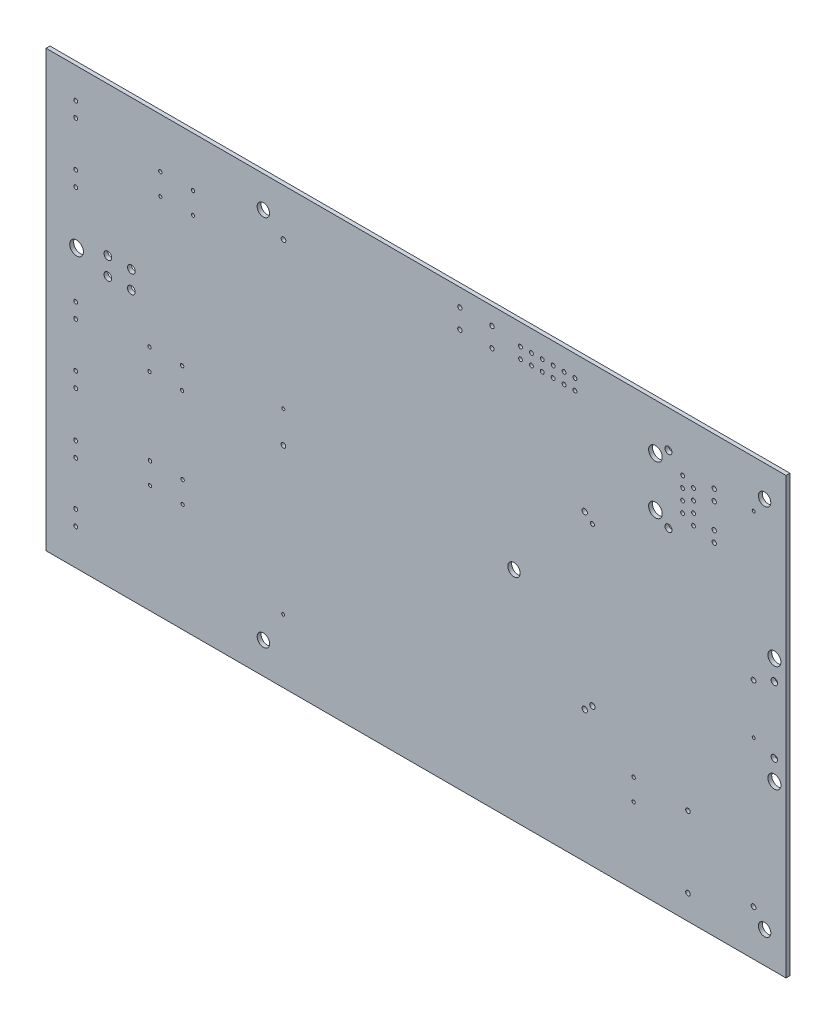
SolidWorks part; units mm, degrees
ref_plane "Front Plane" through (0, 0, 0) normal (0, 0, 1) x (1, 0, 0)
ref_plane "Top Plane" through (0, 0, 0) normal (0, 1, 0) x (1, 0, 0)
ref_plane "Right Plane" through (0, 0, 0) normal (1, 0, 0) x (0, 0, -1)
ref_plane "Plane1" through (0, 0, 0.9093) normal (0, 0, 1) x (1, 0, 0)
sketch "Sketch1" plane through (0, 0, 0.9093) normal (0, 0, 1) x (1, 0, 0)
  line L0 (114.3, 73.66) -> (287.02, 73.66)
  line L1 (287.02, 73.66) -> (287.02, 175.26)
  line L2 (287.02, 175.26) -> (114.3, 175.26)
  line L3 (114.3, 175.26) -> (114.3, 73.66)
  line L4 (114.3, 124.46) -> (287.02, 124.46) construction
  circle A1 centre (279.49, 164.285) radius 0.35
  circle A2 centre (270.256, 164.211) radius 0.51
  circle A3 centre (265.43, 161.925) radius 0.445
  circle A4 centre (262.89, 163.195) radius 0.445
  circle A5 centre (270.256, 161.671) radius 0.51
  circle A6 centre (265.43, 156.845) radius 0.445
  circle A7 centre (265.43, 159.385) radius 0.445
  circle A8 centre (270.256, 155.829) radius 0.51
  circle A9 centre (262.89, 160.655) radius 0.445
  circle A10 centre (262.89, 158.115) radius 0.445
  circle A11 centre (237.744, 167.767) radius 0.45
  circle A12 centre (237.744, 170.307) radius 0.45
  circle A13 centre (235.204, 167.767) radius 0.45
  circle A14 centre (232.664, 170.307) radius 0.45
  circle A15 centre (230.124, 170.307) radius 0.45
  circle A16 centre (235.204, 170.307) radius 0.45
  circle A17 centre (259.588, 166.624) radius 0.815
  circle A18 centre (232.664, 167.767) radius 0.45
  circle A19 centre (256.54, 164.465) radius 1.59
  circle A20 centre (227.584, 167.767) radius 0.45
  circle A21 centre (230.124, 167.767) radius 0.45
  circle A22 centre (284.3022, 136.906) radius 1.524
  circle A23 centre (284.3022, 132.207) radius 0.7493
  circle A24 centre (279.49, 118.485) radius 0.35
  circle A25 centre (270.256, 153.289) radius 0.51
  circle A26 centre (265.43, 154.305) radius 0.445
  circle A27 centre (279.44, 130.085) radius 0.55
  circle A28 centre (284.3022, 112.014) radius 1.524
  circle A29 centre (284.3022, 116.713) radius 0.7493
  circle A30 centre (279.44, 84.285) radius 0.55
  circle A31 centre (264.1346, 79.375) radius 0.5334
  circle A33 centre (262.89, 155.575) radius 0.445
  circle A34 centre (256.54, 153.035) radius 1.59
  circle A35 centre (259.588, 150.876) radius 0.815
  circle A36 centre (240.03, 144.46) radius 0.625
  circle A37 centre (241.83, 142.86) radius 0.475
  circle A38 centre (264.1346, 96.0374) radius 0.5334
  circle A39 centre (251.46, 96.48) radius 0.4
  circle A40 centre (251.46, 91.48) radius 0.375
  circle A41 centre (241.83, 106.06) radius 0.625
  circle A42 centre (240.03, 104.46) radius 0.625
  circle A43 centre (227.584, 170.307) radius 0.45
  circle A44 centre (225.044, 170.307) radius 0.45
  circle A45 centre (225.044, 167.767) radius 0.45
  circle A46 centre (218.38, 171.16) radius 0.495
  circle A47 centre (210.88, 171.16) radius 0.495
  circle A49 centre (218.38, 166.66) radius 0.495
  circle A50 centre (210.88, 166.66) radius 0.495
  circle A51 centre (169.715, 164.285) radius 0.55
  circle A52 centre (148.59, 163.6366) radius 0.4
  circle A53 centre (148.59, 158.6366) radius 0.375
  circle A54 centre (140.97, 163.6366) radius 0.4
  circle A55 centre (121.21, 168.12) radius 0.45
  circle A56 centre (140.97, 158.6366) radius 0.375
  circle A57 centre (121.21, 164.62) radius 0.45
  circle A58 centre (121.21, 154.15) radius 0.45
  circle A59 centre (134.212, 140.53) radius 0.9
  circle A60 centre (128.712, 140.53) radius 0.9
  circle A61 centre (134.212, 136.33) radius 0.9
  circle A62 centre (121.21, 150.65) radius 0.45
  circle A63 centre (121.412, 138.43) radius 1.6
  circle A64 centre (169.69, 122.685) radius 0.55
  circle A65 centre (169.665, 130.085) radius 0.35
  circle A66 centre (146.177, 103.9974) radius 0.4
  circle A67 centre (146.05, 126.96) radius 0.4
  circle A68 centre (138.43, 126.96) radius 0.4
  circle A69 centre (146.05, 121.96) radius 0.375
  circle A70 centre (169.64, 88.485) radius 0.35
  circle A71 centre (146.177, 98.9974) radius 0.375
  circle A73 centre (138.557, 103.9974) radius 0.4
  circle A74 centre (138.557, 98.9974) radius 0.375
  circle A75 centre (128.712, 136.33) radius 0.9
  circle A76 centre (121.21, 127.48) radius 0.45
  circle A77 centre (138.43, 121.96) radius 0.375
  circle A78 centre (121.21, 123.98) radius 0.45
  circle A79 centre (121.21, 113.51) radius 0.45
  circle A80 centre (121.21, 85.57) radius 0.45
  circle A81 centre (121.21, 95.913) radius 0.45
  circle A82 centre (121.21, 82.07) radius 0.45
  circle A83 centre (121.21, 110.01) radius 0.45
  circle A84 centre (121.21, 99.413) radius 0.45
extrude "Boss-Extrude1" add sketch "Sketch1" against normal blind 0.9093
hole_wizard "M2.5 Clearance Hole1" positions "Sketch3" profile "Sketch2" hole size "M2.5" standard "Ansi Metric"
sketch "Sketch3" plane through (0, 0, 0.9093) normal (0, 0, 1) x (1, 0, 0)
  line L0 (114.3, 124.46) -> (287.02, 124.46) construction
  line L1 (114.3, 175.26) -> (114.3, 73.66) construction
  line L2 (287.02, 73.66) -> (287.02, 175.26) construction
  line L5 (282.02, 167.96) -> (165.02, 167.96)
  line L6 (282.02, 167.96) -> (282.02, 80.96)
  line L7 (282.02, 80.96) -> (165.02, 80.96)
  line L8 (165.02, 167.96) -> (165.02, 80.96)
  line L9 (282.02, 167.96) -> (165.02, 80.96) construction
  line L10 (282.02, 80.96) -> (165.02, 167.96) construction
  point P0 (282.02, 167.96)
  point P1 (282.02, 80.96)
  point P3 (165.02, 80.96)
  point P5 (165.02, 167.96)
  point P16 (223.52, 124.46)
  dimension "D1" = 117
  dimension "D2" = 87
  dimension "D3" = 63.5
sketch "Sketch2" plane through (282.02, 167.96, 0.9093) normal (1, 0, 0) x (0, -1, 0)
  line L0 (0, 0) -> (0, 26.2712)
  line L1 (0, 26.2712) -> (1.45, 25.4)
  line L2 (1.45, 25.4) -> (1.45, 0)
  line L5 (1.45, 0) -> (0, 0)
  line L10 (0, 26.2712) -> (-1.45, 25.4) construction
  line L11 (0, -6.35) -> (0, 107.95) construction
  dimension "Hole Dia." = 2.9
  dimension "Hole Depth" = 25.4
  dimension "Drill Angle" = 118
